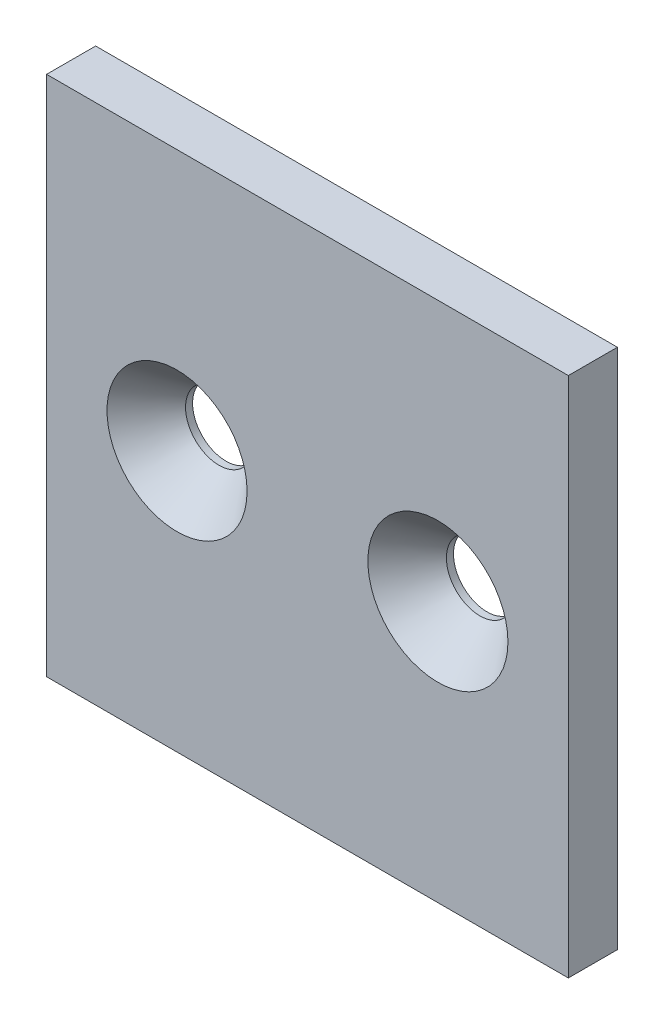
SolidWorks part; units mm, degrees
ref_plane "Front Plane" through (0, 0, 0) normal (0, 0, 1) x (1, 0, 0)
ref_plane "Top Plane" through (0, 0, 0) normal (0, 1, 0) x (1, 0, 0)
ref_plane "Right Plane" through (0, 0, 0) normal (1, 0, 0) x (0, 0, -1)
sketch "Sketch1" plane through (0, 0, 0) normal (0, 0, 1) x (1, 0, 0)
  line L0 (0, 0) -> (0, 50.8)
  line L1 (12.7, 25.4) -> (38.1, 25.4) construction
  line L4 (50.8, 50.8) -> (0, 50.8)
  line L5 (50.8, 0) -> (0, 0)
  line L7 (50.8, 50.8) -> (50.8, 0)
  circle A0 centre (12.7, 25.4) radius 3.2639
  circle A1 centre (38.1, 25.4) radius 3.2639
  dimension "D1" = 25.4
  dimension "E" = 6.5278
  dimension "D2" = 12.7
  dimension "C" = 50.8
  dimension "D3" = 25.4
  dimension "B" = 50.8
extrude "Boss-Extrude1" add sketch "Sketch1" along normal mid plane 4.7752
sketch "Sketch2" plane through (0, 0, 2.3876) normal (0, 0, 1) x (1, 0, 0)
  circle A0 centre (12.7, 25.4) radius 3.2639 construction
  circle A1 centre (12.7, 25.4) radius 3.2639
  circle A2 centre (38.1, 25.4) radius 3.2639 construction
  circle A3 centre (38.1, 25.4) radius 3.2639
extrude "Cut-Extrude1" cut sketch "Sketch2" along normal through all draft 41 from offset 4.0894
